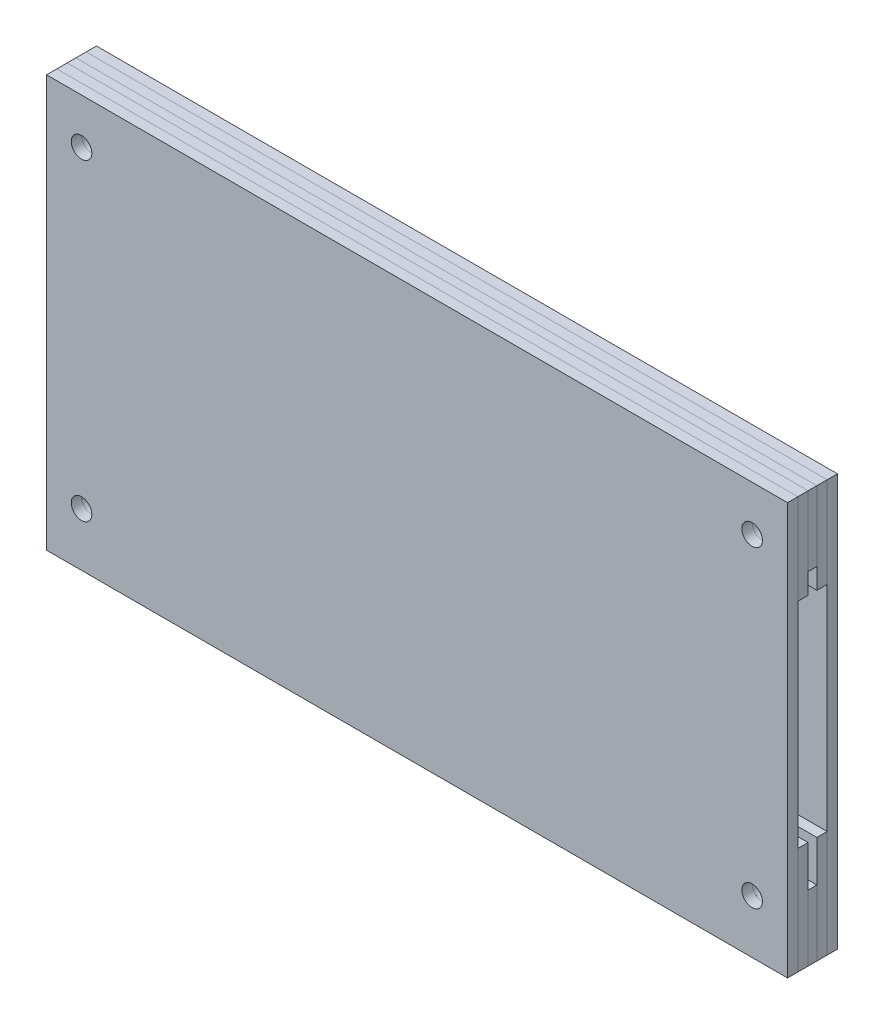
SolidWorks part; units mm, degrees
ref_plane "Front" through (0, 0, 0) normal (0, 0, 1) x (1, 0, 0)
ref_plane "Top" through (0, 0, 0) normal (0, 1, 0) x (1, 0, 0)
ref_plane "Right" through (0, 0, 0) normal (1, 0, 0) x (0, 0, -1)
sketch "Sketch1" plane through (0, 0, 0) normal (0, 0, 1) x (1, 0, 0)
  line L1 (-114.3, 63.5) -> (114.3, 63.5)
  line L2 (-114.3, 63.5) -> (-114.3, -63.5)
  line L3 (-114.3, -63.5) -> (114.3, -63.5)
  line L4 (114.3, 63.5) -> (114.3, -63.5)
  line L5 (-114.3, 63.5) -> (114.3, -63.5) construction
  line L6 (-114.3, -63.5) -> (114.3, 63.5) construction
  point P4 (0, 0)
  dimension "D1" = 228.6
  dimension "D2" = 127
extrude "Boss-Extrude1" add sketch "Sketch1" along normal blind 3.175
sketch "Sketch2" plane through (0, 0, 0) normal (0, 0, -1) x (-1, 0, 0)
  line L1 (-114.3, 35.56) -> (-114.3, 63.5)
  line L2 (-114.3, -63.5) -> (-114.3, 63.5) construction
  line L3 (-114.3, 63.5) -> (114.3, 63.5)
  line L4 (114.3, 63.5) -> (114.3, -63.5)
  line L5 (114.3, -63.5) -> (92.1734, -63.5)
  line L6 (114.3, -63.5) -> (-114.3, -63.5) construction
  line L9 (92.71, -30.48) -> (-114.3, -30.48)
  line L10 (-114.3, -30.48) -> (-114.3, -63.5)
  line L11 (-114.3, -63.5) -> (92.1734, -63.5)
  line L12 (-114.3, 35.56) -> (92.71, 35.56)
  line L13 (92.71, 35.56) -> (92.71, -30.48)
  point P16 (4.4481, 11.7339)
  dimension "D1" = 21.59
  dimension "D2" = 66.04
  dimension "D3" = 30.48
extrude "Boss-Extrude2" add sketch "Sketch2" along normal blind 3.175 separate body
sketch "Sketch4" plane through (0, 0, -3.175) normal (0, 0, -1) x (-1, 0, 0)
  line L10 (-114.3, 41.91) -> (101.6, 41.91)
  line L11 (101.6, 41.91) -> (101.6, -43.18)
  line L12 (101.6, -43.18) -> (-114.3, -43.18)
  line L13 (-114.3, -43.18) -> (-114.3, -63.5)
  line L14 (-114.3, -63.5) -> (114.3, -63.5) construction
  line L15 (-114.3, -63.5) -> (114.3, -63.5)
  line L16 (114.3, -63.5) -> (114.3, 63.5)
  line L17 (114.3, 63.5) -> (-114.3, 63.5)
  line L18 (114.3, 63.5) -> (-114.3, 63.5) construction
  line L19 (-114.3, 63.5) -> (-114.3, 41.91)
  line L21 (-114.3, 35.56) -> (92.71, 35.56) construction
  line L22 (92.71, -30.48) -> (-114.3, -30.48) construction
  line L23 (-114.3, -30.48) -> (-114.3, -63.5) construction
  dimension "D1" = 12.7
  dimension "D2" = 6.35
  dimension "D3" = 12.7
extrude "Boss-Extrude4" add sketch "Sketch4" along normal blind 2.7051 separate body
ref_plane "Plane1" through (0, 0, -4.5275) normal (0, 0, -1) x (-1, 0, 0)
mirror "Mirror1" about plane through (0, 0, -4.5275) normal (0, 0, -1) of bodies 101 102
sketch "Sketch6" plane through (0, 0, 0) normal (0, 0, 1) x (1, 0, 0)
  line L0 (-103.505, 63.5) -> (-103.505, -63.5) construction
  line L1 (-114.3, 63.5) -> (114.3, 63.5) construction
  line L2 (114.3, -63.5) -> (-114.3, -63.5) construction
  line L3 (-103.505, 0) -> (-92.71, 0) construction
  line L4 (-92.71, 35.56) -> (-92.71, -30.48) construction
  line L5 (-103.505, 0) -> (-114.3, 0) construction
  line L6 (-114.3, -63.5) -> (-114.3, 63.5) construction
  line L7 (-114.3, 49.53) -> (114.3, 49.53) construction
  line L8 (114.3, 63.5) -> (114.3, 35.56) construction
  line L9 (0, 49.53) -> (0, 63.5) construction
  line L10 (0, 49.53) -> (0, 35.56) construction
  line L11 (114.3, 35.56) -> (-92.71, 35.56) construction
  line L12 (-114.3, -46.99) -> (114.3, -46.99) construction
  line L13 (114.3, -30.48) -> (114.3, -63.5) construction
  line L14 (0, -46.99) -> (0, -30.48) construction
  line L15 (-92.71, -30.48) -> (114.3, -30.48) construction
  line L16 (0, -46.99) -> (0, -63.5) construction
  line L17 (103.378, 63.5) -> (103.378, -63.5) construction
  circle A0 centre (-103.505, 49.53) radius 3.175
  circle A1 centre (-103.505, -46.99) radius 3.175
  circle A2 centre (103.378, 49.53) radius 3.175
  circle A3 centre (103.378, -46.99) radius 3.175
  dimension "D1" = 6.35
  dimension "D2" = 10.922
extrude "Cut-Extrude1" cut sketch "Sketch6" against normal through all both and the other way through all contours A0 | A1 | A2 | A3
